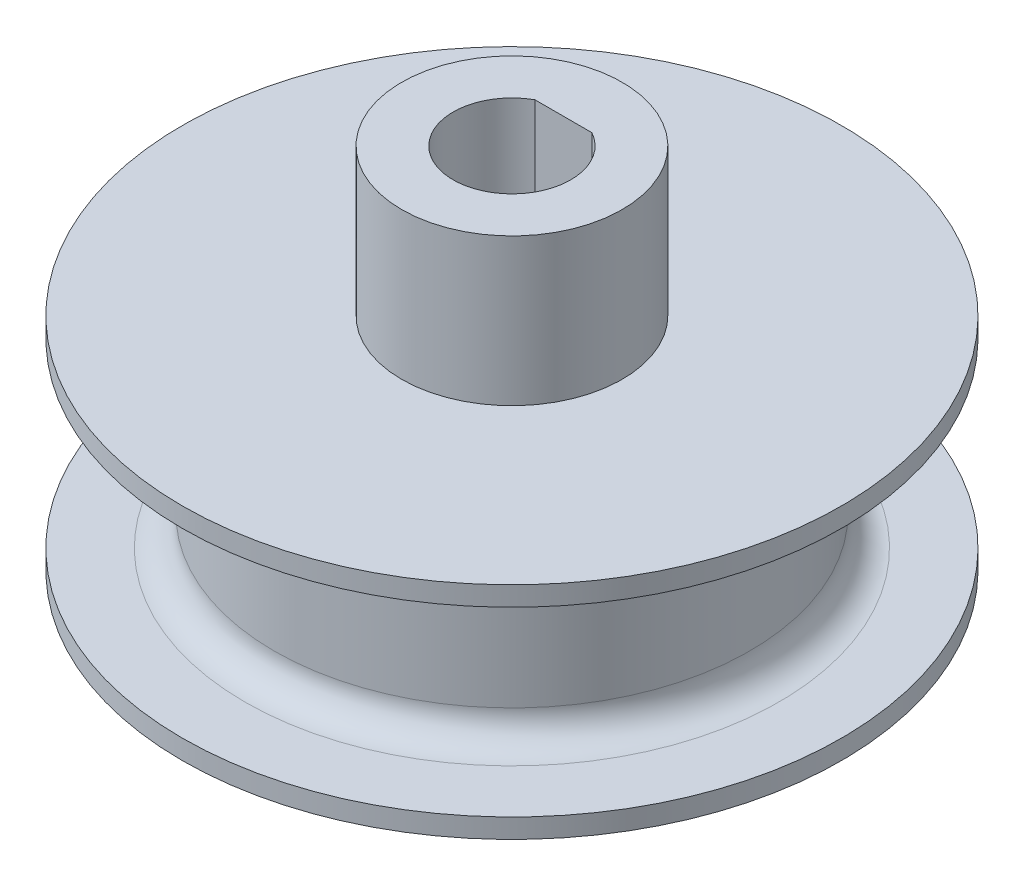
SolidWorks part; units mm, degrees
ref_plane "Front Plane" through (0, 0, 0) normal (0, 0, 1) x (1, 0, 0)
ref_plane "Top Plane" through (0, 0, 0) normal (0, 1, 0) x (1, 0, 0)
ref_plane "Right Plane" through (0, 0, 0) normal (1, 0, 0) x (0, 0, -1)
sketch "Sketch2" plane through (0, 0, 0) normal (0, 1, 0) x (1, 0, 0)
  line L0 (1.9365, 3.5) -> (-1.9365, 3.5)
  line L1 (0, 3.5) -> (0, -4)
  circle A0 centre (0, 0) radius 4
  circle A1 centre (0, 0) radius 15
  dimension "D1" = 8
  dimension "D3" = 30
  dimension "D2" = 7.5
extrude "Boss-Extrude1" add sketch "Sketch2" along normal mid plane 15 contours A1 A0 | L0 A0
sketch "Sketch3" plane through (0, 0, 0) normal (1, 0, 0) x (0, 0, -1)
  line L0 (15, 7.5) -> (22.4137, 7.5)
  line L1 (22.4137, 7.5) -> (22.4137, 6.176)
  line L2 (22.4137, 6.176) -> (18.1595, 6.176)
  line L3 (16.1595, 4.176) -> (16.1595, -4.176)
  line L4 (18.1595, -6.176) -> (22.4137, -6.176)
  line L5 (22.4137, -6.176) -> (22.4137, -7.5)
  line L6 (22.4137, -7.5) -> (15, -7.5)
  line L7 (15, -7.5) -> (15, 7.5)
  line L8 (0, 7.5) -> (0, -7.5)
  line L9 (15, 7.5) -> (-15, 7.5) construction
  arc A0 (16.1595, -4.176) -> (18.1595, -6.176) centre (18.1595, -4.176) ccw
  arc A1 (18.1595, 6.176) -> (16.1595, 4.176) centre (18.1595, 4.176) ccw
  dimension "D1" = 2
revolve "Revolve1" add sketch "Sketch3" angle 360 about L8
sketch "Sketch4" plane through (0, 7.5, 0) normal (0, 1, 0) x (1, 0, 0)
  line L0 (-1.9365, 3.5) -> (1.9365, 3.5)
  circle A0 centre (0, 0) radius 4
  circle A1 centre (0, 0) radius 7.5
  arc M2 (1.9365, 3.5) -> (-1.9365, 3.5) centre (0, 0) cw
  line M3 (-1.9365, 3.5) -> (1.9365, 3.5)
  dimension "D1" = 15
extrude "Boss-Extrude2" add sketch "Sketch4" along normal blind 10 contours A1 A0 M2 | A0 M3
